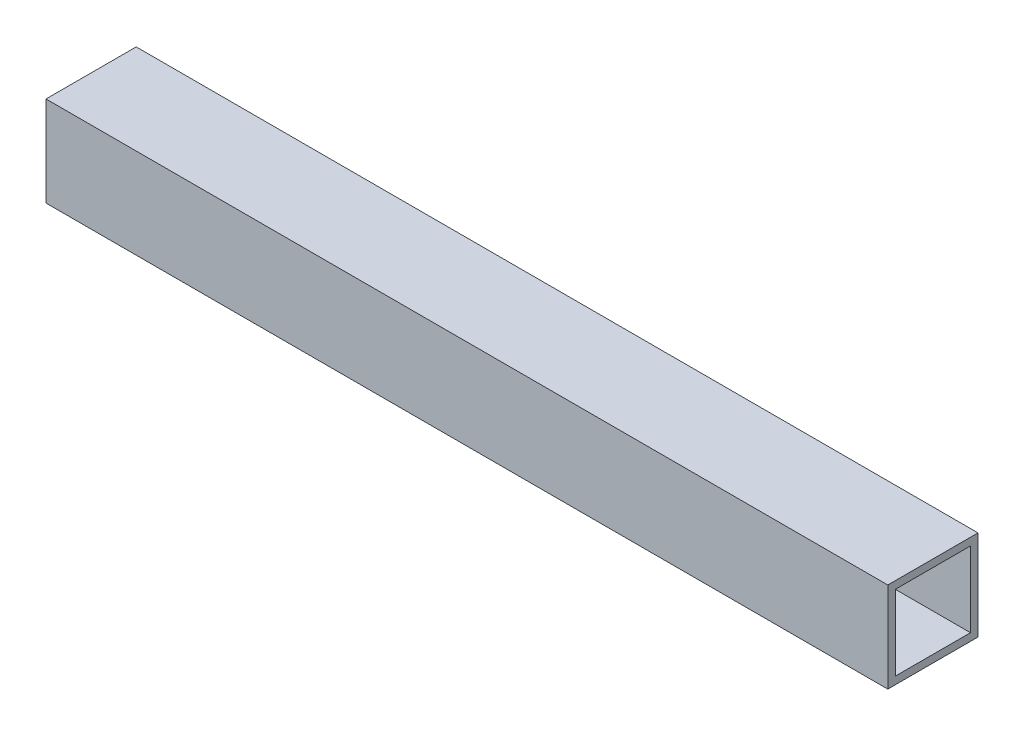
SolidWorks part; units mm, degrees
ref_plane "Front Plane" through (0, 0, 0) normal (0, 0, 1) x (1, 0, 0)
ref_plane "Top Plane" through (0, 0, 0) normal (0, 1, 0) x (1, 0, 0)
ref_plane "Right Plane" through (0, 0, 0) normal (1, 0, 0) x (0, 0, -1)
sketch "Sketch1" plane through (0, 0, 0) normal (1, 0, 0) x (0, -1, 0)
  line L1 (-9.525, 9.525) -> (9.525, 9.525)
  line L2 (-9.525, 9.525) -> (-9.525, -9.525)
  line L3 (-9.525, -9.525) -> (9.525, -9.525)
  line L4 (9.525, 9.525) -> (9.525, -9.525)
  line L5 (-9.525, 9.525) -> (9.525, -9.525) construction
  line L6 (-9.525, -9.525) -> (9.525, 9.525) construction
  line L7 (-7.9375, 7.9375) -> (7.9375, 7.9375)
  line L8 (-7.9375, 7.9375) -> (-7.9375, -7.9375)
  line L9 (-7.9375, -7.9375) -> (7.9375, -7.9375)
  line L10 (7.9375, 7.9375) -> (7.9375, -7.9375)
  line L11 (-7.9375, 7.9375) -> (7.9375, -7.9375) construction
  line L12 (-7.9375, -7.9375) -> (7.9375, 7.9375) construction
  point P0 (0, 0)
  point P5 (0, 0)
  dimension "D2" = 19.05
  dimension "D1" = 15.875
extrude "Boss-Extrude1" add sketch "Sketch1" along normal mid plane 177.8
equation "\"Height\"= 32in"
equation "\"Width\"= 23in"
equation "\"Depth\"= 20in"
equation "\"Plexi\"= .121in"
equation "\"MagnetThickness\"= .125in"
equation "\"MagnetDiameter\"= 12mm"
equation "\"DoorPlexi\" = \"Plexi\""
equation "\"BasePlateThickness\" = 0.5in"
equation "\"BasePlateWidth\" = \"Width\"+\"EBWidth\"-2*\"Plexi\""
equation "\"BasePlateDepth\" = \"TopBarDepth\"+2*\"CornerCube\""
equation "\"Boxsize\" = .75in"
equation "\"BoxsizeHalf\" = \"Boxsize\"/2"
equation "\"Boxinner\" = .625in"
equation "\"CornerCube\" = 0.75in"
equation "\"FingerLength\" = 1.125in"
equation "\"FingerWidth\" = .625in"
equation "\"Cutwidth\"= .016in"
equation "\"Earsize\"= 1in + \"Cutwidth\" /2"
equation "\"Slotsize\" = 1in - \"CutWidth\" / 2"
equation "\"InnerWidth\" = \"Width\" - 2* \"Plexi\""
equation "\"InnerHeight\" = \"Height\" -2 * \"Plexi\""
equation "\"InnerDepth\" = \"Depth\" - 2*\"Plexi\""
equation "\"RearNumHoles\" = 4"
equation "\"RearHolesBorder\" = 2.25"
equation "\"RearHoleSpacing\" = (\"Width\" - 2*\"RearHolesBorder\") / (\"RearNumHoles\"-1)"
equation "\"RearBarLength\" = (\"InnerWidth\"-2*\"CornerCube\")"
equation "\"RearTopNumHoles\" = 4"
equation "\"RearTopHolesBorder\" = 3.1"
equation "\"RearTopHolesSpacing\" = (\"Width\" - 2*\"RearTopHolesBorder\") / (\"RearTopNumHoles\"-1)"
equation "\"SideTopNumHoles\" = 4"
equation "\"SideTopHoleOffset\"=\"CornerCube\"+\"FingerLength\"+\"Plexi\"+.5"
equation "\"SideHorizNumHoles\" = 4"
equation "\"SideHorizHoleBorder\" = 1.50"
equation "\"SideVertBarLength\"=\"Height\"-\"BasePlateThickness\"-2*\"CornerCube\"-\"Plexi\""
equation "\"SideVertNumHoles\" = 4"
equation "\"SideVertHolesBorder\" = \"CornerCube\"+\"FingerLength\"+1.50"
equation "\"SideVertHoleSpacing\" = (\"InnerHeight\" - 2*\"SideVertHolesBorder\") / (\"SideVertNumHoles\"-1)"
equation "\"RearSideVertNumHoles\" = 4"
equation "\"RearSideVertHolesBorder\" = 2.4"
equation "\"RearSideVertHoleSpacing\" = (\"InnerHeight\" - 2*\"RearSideVertHolesBorder\") / (\"RearSideVertNumHoles\"-1)"
equation "\"RivetDia\" = .228in"
equation "\"SlotDepth\" = \"Plexi\" + 0.75in + .005in"
equation "\"SideSlotWidth\"   = \"Plexi\"+.005in"
equation "\"SidePanelVertSpacing\" = (\"Height\"-2*(1.75-\"Plexi\")) / 5"
equation "\"BottomPanelSideHoleSpacing\" = (\"InnerDepth\"-2*(1.75-\"Plexi\")) / 4"
equation "\"FrontDoorGap\" = .1in"
equation "\"TopDepth\" = \"Depth\"-\"DoorPlexi\"-\"FrontDoorGap\""
equation "\"TopBarDepth\" = \"Depth\"-\"DoorPlexi\"-\"Plexi\"-2*\"MagnetThickness\"-2*\"CornerCube\""
equation "\"CoolerDepth\" = 12in"
equation "\"ShelfDepth\" = \"TopBarDepth\"+\"CornerCube\"-\"CoolerDepth\""
equation "\"ShelfBarWidth\" = \"EBWidth\"-\"Boxsize\""
equation "\"IntakeWidth\"=4in"
equation "\"IntakeHeight\"=2in"
equation "\"ExhaustWidth\"=4in"
equation "\"ExhaustHeight\"=2in"
equation "\"VentSpacing\"=7in"
equation "\"SideTopHoleSpacing\" = (\"TopBarDepth\"-2*\"SideTopHoleOffset\") / (\"SideTopNumHoles\"-1)"
equation "\"SideHorizHoleSpacing\" = (\"TopBarDepth\"-2*\"SideHorizHoleBorder\") / (\"SideHorizNumHoles\"-1)"
equation "\"ShelfBarWidthShort\" = \"ShelfBarWidth\"-\"Boxsize\"-\"ShelfGap\""
equation "\"D1@Boss-Extrude1\"=\"ShelfBarWidthShort\""
equation "\"D2@Sketch1\"=\"Boxsize\""
equation "\"D1@Sketch1\"=\"Boxinner\""
equation "\"EBWidth\" = 9in"
equation "\"ShelfBarDepth\"=\"ShelfDepth\"-2*\"CornerCube\""
equation "\"ShelfGap\" = 0.5in"
equation "\"AngleBracketLength\"=20mm"
equation "\"AngleBracketWidth\"=.5in"
equation "\"AngleBracketThickness\"=.125in"
equation "\"AngleBracketHolePos\"=15mm"
equation "\"AngleBracketHoleDia\"=\"Rivet3_16Dia\""
equation "\"ShelfBarAngleHole\"=\"ShelfGap\"+\"Boxsize\"+\"AngleBracketHolePosShort\""
equation "\"ShelfWidth\" = \"EBWidth\"-\"ShelfGap\""
